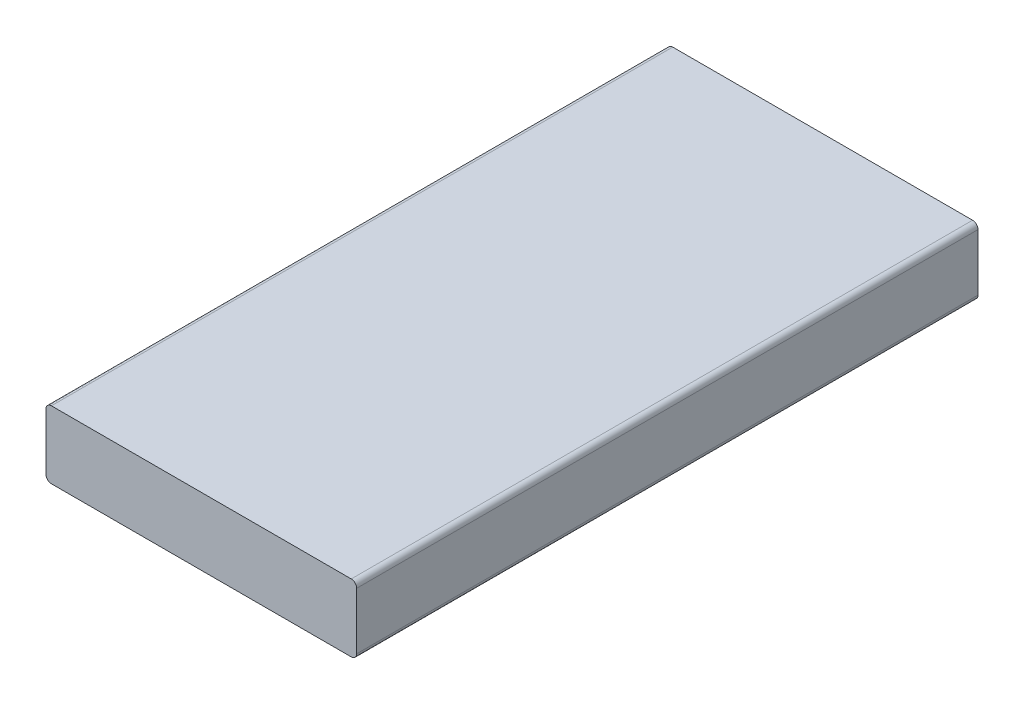
SolidWorks part; units mm, degrees
material "Polyurethane Foam Rigid"
ref_plane "Front Plane" through (0, 0, 0) normal (0, 0, 1) x (1, 0, 0)
ref_plane "Top Plane" through (0, 0, 0) normal (0, 1, 0) x (1, 0, 0)
ref_plane "Right Plane" through (0, 0, 0) normal (1, 0, 0) x (0, 0, -1)
sketch "Sketch1" plane through (0, 0, 0) normal (0, 0, 1) x (1, 0, 0)
  line L1 (-29.3403, 15.8854) -> (85.6597, 15.8854)
  line L2 (-29.3403, 15.8854) -> (-29.3403, -9.1146)
  line L3 (-29.3403, -9.1146) -> (85.6597, -9.1146)
  line L4 (85.6597, 15.8854) -> (85.6597, -9.1146)
  dimension "D1" = 25
  dimension "D2" = 115
extrude "Boss-Extrude1" add sketch "Sketch1" against normal blind 230
fillet "Fillet1" radius 2 4 edges at (85.6597, -9.1146, -115) (85.6597, 15.8854, -115) (-29.3403, -9.1146, -115) (-29.3403, 15.8854, -115)
